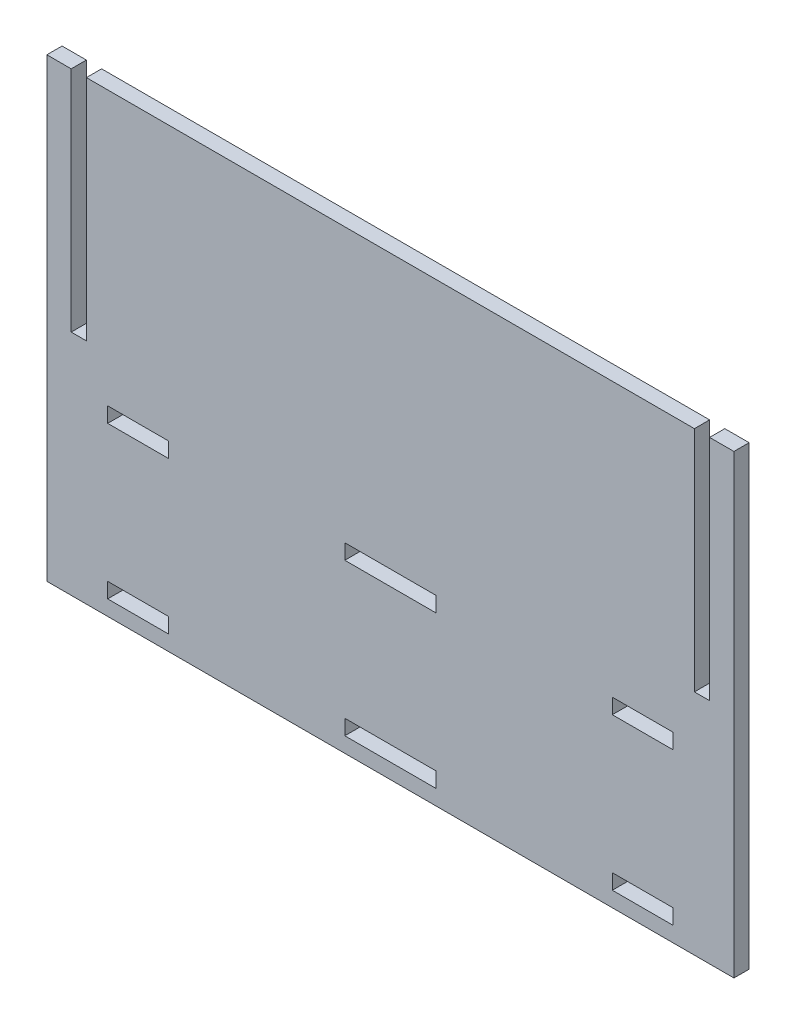
SolidWorks part; units mm, degrees
ref_plane "Plan de face" through (0, 0, 0) normal (0, 0, 1) x (1, 0, 0)
ref_plane "Plan de dessus" through (0, 0, 0) normal (0, 1, 0) x (1, 0, 0)
ref_plane "Plan de droite" through (0, 0, 0) normal (1, 0, 0) x (0, 0, -1)
sketch "Esquisse1" plane through (0, 0, 0) normal (0, 0, 1) x (1, 0, 0)
  line L0 (0, 150) -> (0, 0) construction
  line L1 (73, 10) -> (93, 10)
  line L2 (73, 60) -> (93, 60)
  line L3 (73, 60) -> (73, 55)
  line L4 (73, 55) -> (93, 55)
  line L5 (-100, 150) -> (100, 150)
  line L6 (100, 150) -> (100, 75)
  line L7 (100, 75) -> (105, 75)
  line L8 (105, 75) -> (105, 150)
  line L9 (105, 150) -> (113, 150)
  line L10 (113, 150) -> (113, 0)
  line L11 (113, 0) -> (-113, 0)
  line L12 (93, 60) -> (93, 55)
  line L13 (73, 10) -> (73, 5)
  line L14 (73, 5) -> (93, 5)
  line L15 (93, 10) -> (93, 5)
  line L16 (-15, 5) -> (15, 5)
  line L17 (15, 5) -> (15, 10)
  line L18 (15, 10) -> (0, 10)
  line L19 (-15, 60) -> (0, 60)
  line L20 (0, 100) -> (0, -50) construction
  line L21 (-15, 55) -> (15, 55)
  line L22 (15, 55) -> (15, 60)
  line L23 (15, 60) -> (0, 60)
  line L24 (-15, 55) -> (-15, 60)
  line L25 (113, 100) -> (113, -50) [skipped]
  line L26 (-15, 10) -> (0, 10)
  line L27 (-15, 5) -> (-15, 10)
  line L28 (-93, 10) -> (-93, 5)
  line L29 (-73, 5) -> (-93, 5)
  line L30 (-73, 10) -> (-73, 5)
  line L31 (-93, 60) -> (-93, 55)
  line L32 (-113, 150) -> (-113, 0)
  line L33 (-105, 150) -> (-113, 150)
  line L34 (-105, 75) -> (-105, 150)
  line L35 (-100, 75) -> (-105, 75)
  line L36 (-100, 150) -> (-100, 75)
  line L37 (-73, 55) -> (-93, 55)
  line L38 (-73, 60) -> (-73, 55)
  line L39 (-73, 60) -> (-93, 60)
  line L40 (-73, 10) -> (-93, 10)
  point P33 (0, 55)
  point P36 (0, 5)
  point P50 (0, 0)
  dimension "D2" = 150
  dimension "D3" = 75
  dimension "D4" = 20
  dimension "D5" = 8
  dimension "D6" = 5
  dimension "D7" = 5
  dimension "D8" = 20
  dimension "D9" = 55
  dimension "D10" = 15
  dimension "D11" = 5
  dimension "D12" = 100
  dimension "D13" = 2
extrude "Boss.-Extru.1" add sketch "Esquisse1" along normal blind 5
